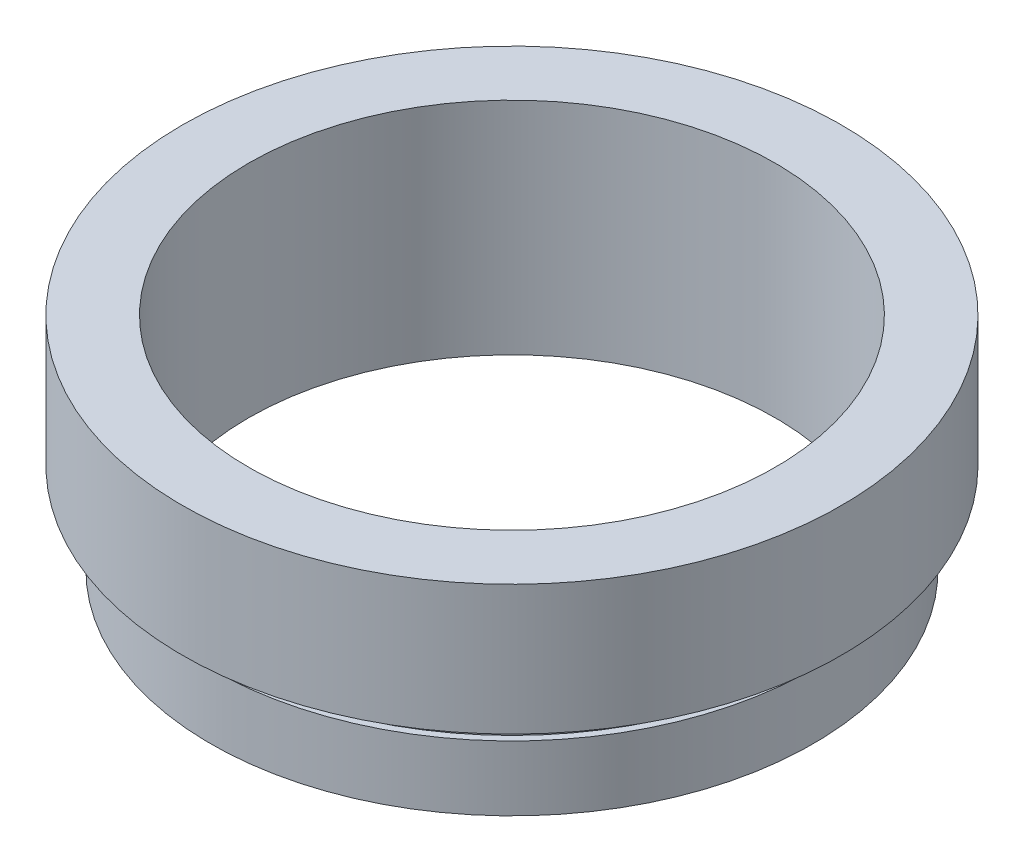
SolidWorks part; units mm, degrees
ref_plane "前视基准面" through (0, 0, 0) normal (0, 0, 1) x (1, 0, 0)
ref_plane "上视基准面" through (0, 0, 0) normal (0, 1, 0) x (1, 0, 0)
ref_plane "右视基准面" through (0, 0, 0) normal (1, 0, 0) x (0, 0, -1)
sketch "草图1" plane through (0, 0, 0) normal (0, 0, 1) x (1, 0, 0)
  line L0 (0, 16.886) -> (0, -24.4878) construction
  line L1 (10.15, -0.5455) -> (10.15, 7.9545)
  line L2 (12.7, 7.9545) -> (12.7, 2.9545)
  line L3 (10.15, 7.9545) -> (12.7, 7.9545)
  line L4 (11.35, 2.9545) -> (11.35, 1.9545)
  line L5 (11.35, 2.9545) -> (12.7, 2.9545)
  line L7 (11.61, 1.9545) -> (11.61, -0.5455)
  line L8 (11.35, 1.9545) -> (11.61, 1.9545)
  line L9 (10.15, -0.5455) -> (11.61, -0.5455)
  dimension "D1" = 10.15
  dimension "D2" = 12.7
  dimension "D3" = 5
  dimension "D4" = 8.5
  dimension "D5" = 11.35
  dimension "D6" = 1
  dimension "D7" = 11.61
revolve "旋转1" add sketch "草图1" angle 360 about L0
cosmetic thread "装饰螺纹线1" parameters "D2"=23.2
cosmetic thread "装饰螺纹线2" parameters "D2"=20.32
